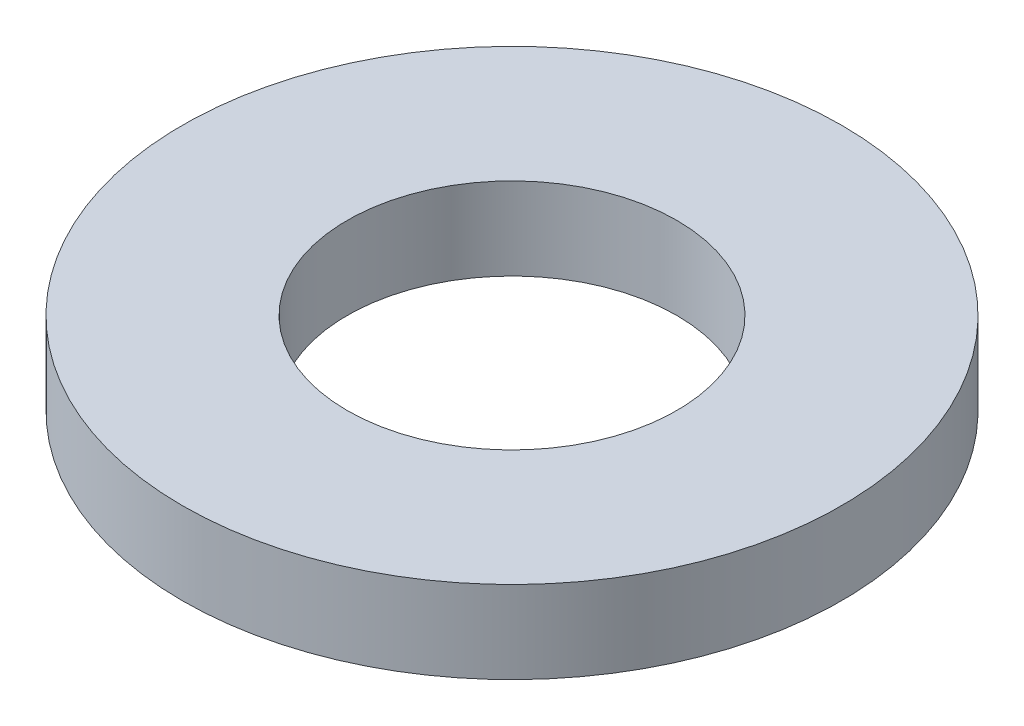
SolidWorks part; units mm, degrees
ref_plane "Front Plane" through (0, 0, 0) normal (0, 0, 1) x (1, 0, 0)
ref_plane "Top Plane" through (0, 0, 0) normal (0, 1, 0) x (1, 0, 0)
ref_plane "Right Plane" through (0, 0, 0) normal (1, 0, 0) x (0, 0, -1)
sketch "Sketch1" plane through (0, 0, 0) normal (0, 1, 0) x (1, 0, 0)
  circle A0 centre (0, 0) radius 4
  circle A1 centre (0, 0) radius 2
  dimension "D1" = 8
  dimension "D2" = 4
extrude "Boss-Extrude1" add sketch "Sketch1" along normal blind 1
